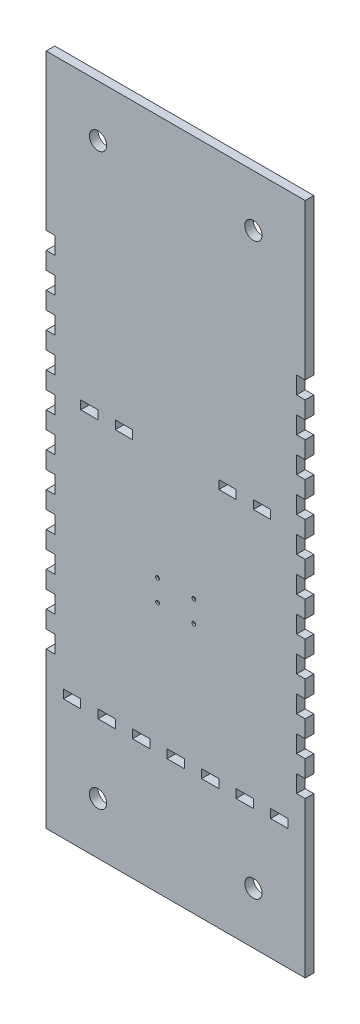
SolidWorks part; units mm, degrees
material "Balsa"
ref_plane "Alzado" through (0, 0, 0) normal (0, 0, 1) x (1, 0, 0)
ref_plane "Planta" through (0, 0, 0) normal (0, 1, 0) x (1, 0, 0)
ref_plane "Vista lateral" through (0, 0, 0) normal (1, 0, 0) x (0, 0, -1)
sketch "Croquis1" plane through (0, 0, 0) normal (0, 0, 1) x (1, 0, 0)
  line L0 (75, 0) -> (-75, 0) construction
  line L1 (75, -195) -> (-75, -195)
  line L2 (75, -195) -> (75, 195)
  line L3 (75, 195) -> (-75, 195)
  line L4 (-75, -195) -> (-75, 195)
  line L5 (75, -195) -> (-75, 195) construction
  line L6 (75, 195) -> (-75, -195) construction
  circle A0 centre (-45, 165) radius 5
  circle A1 centre (45, 165) radius 5
  circle A2 centre (-45, -165) radius 5
  circle A3 centre (45, -165) radius 5
  point P0 (0, 0)
  dimension "D3" = 10
  dimension "D8" = 10
  dimension "D1" = 150
  dimension "D2" = 390
  dimension "D4" = 30
  dimension "D5" = 30
  dimension "D6" = 30
  dimension "D7" = 30
extrude "Saliente-Extruir1" add sketch "Croquis1" along normal blind 5
sketch "Croquis3" plane through (0, 0, 0) normal (0, 0, -1) x (-1, 0, 0)
  line L0 (-75, -195) -> (-75, 195) construction
  line L1 (-75, 105) -> (-70, 105)
  line L2 (-75, 105) -> (-75, 95)
  line L3 (-75, 95) -> (-70, 95)
  line L4 (-70, 105) -> (-70, 95)
  line L5 (-75, 195) -> (75, 195) construction
  line L6 (-75, 85) -> (-75, 75)
  line L7 (-75, 85) -> (-70, 85)
  line L8 (-70, 85) -> (-70, 75)
  line L9 (-75, 75) -> (-70, 75)
  line L10 (-75, 65) -> (-75, 55)
  line L11 (-75, 65) -> (-70, 65)
  line L12 (-70, 65) -> (-70, 55)
  line L13 (-75, 55) -> (-70, 55)
  line L14 (-75, 45) -> (-75, 35)
  line L15 (-75, 45) -> (-70, 45)
  line L16 (-70, 45) -> (-70, 35)
  line L17 (-75, 35) -> (-70, 35)
  line L18 (-75, 25) -> (-75, 15)
  line L19 (-75, 25) -> (-70, 25)
  line L20 (-70, 25) -> (-70, 15)
  line L21 (-75, 15) -> (-70, 15)
  line L22 (-75, 5) -> (-75, -5)
  line L23 (-75, 5) -> (-70, 5)
  line L24 (-70, 5) -> (-70, -5)
  line L25 (-75, -5) -> (-70, -5)
  line L26 (-75, -15) -> (-75, -25)
  line L27 (-75, -15) -> (-70, -15)
  line L28 (-70, -15) -> (-70, -25)
  line L29 (-75, -25) -> (-70, -25)
  line L30 (-75, -35) -> (-75, -45)
  line L31 (-75, -35) -> (-70, -35)
  line L32 (-70, -35) -> (-70, -45)
  line L33 (-75, -45) -> (-70, -45)
  line L34 (-75, -55) -> (-75, -65)
  line L35 (-75, -55) -> (-70, -55)
  line L36 (-70, -55) -> (-70, -65)
  line L37 (-75, -65) -> (-70, -65)
  line L38 (-75, -75) -> (-75, -85)
  line L39 (-75, -75) -> (-70, -75)
  line L40 (-70, -75) -> (-70, -85)
  line L41 (-75, -85) -> (-70, -85)
  line L42 (-75, -95) -> (-75, -105)
  line L43 (-75, -95) -> (-70, -95)
  line L44 (-70, -95) -> (-70, -105)
  line L45 (-75, -105) -> (-70, -105)
  line L47 (-98.3206, -125) -> (133.2182, -125) construction
  line L48 (75, -105) -> (70, -105)
  line L49 (70, -95) -> (70, -105)
  line L50 (75, -95) -> (70, -95)
  line L51 (75, -95) -> (75, -105)
  line L52 (75, -85) -> (70, -85)
  line L53 (70, -75) -> (70, -85)
  line L54 (75, -75) -> (70, -75)
  line L55 (75, -75) -> (75, -85)
  line L56 (75, -65) -> (70, -65)
  line L57 (70, -55) -> (70, -65)
  line L58 (75, -55) -> (70, -55)
  line L59 (75, -55) -> (75, -65)
  line L60 (75, -45) -> (70, -45)
  line L61 (70, -35) -> (70, -45)
  line L62 (75, -35) -> (70, -35)
  line L63 (75, -35) -> (75, -45)
  line L64 (75, -25) -> (70, -25)
  line L65 (70, -15) -> (70, -25)
  line L66 (75, -15) -> (70, -15)
  line L67 (75, -15) -> (75, -25)
  line L68 (75, -5) -> (70, -5)
  line L69 (70, 5) -> (70, -5)
  line L70 (75, 5) -> (70, 5)
  line L71 (75, 5) -> (75, -5)
  line L72 (75, 15) -> (70, 15)
  line L73 (70, 25) -> (70, 15)
  line L74 (75, 25) -> (70, 25)
  line L75 (75, 25) -> (75, 15)
  line L76 (75, 35) -> (70, 35)
  line L77 (70, 45) -> (70, 35)
  line L78 (75, 45) -> (70, 45)
  line L79 (75, 45) -> (75, 35)
  line L80 (75, 55) -> (70, 55)
  line L81 (70, 65) -> (70, 55)
  line L82 (75, 65) -> (70, 65)
  line L83 (75, 65) -> (75, 55)
  line L84 (75, 75) -> (70, 75)
  line L85 (70, 85) -> (70, 75)
  line L86 (75, 85) -> (70, 85)
  line L87 (75, 85) -> (75, 75)
  line L88 (70, 105) -> (70, 95)
  line L89 (75, 95) -> (70, 95)
  line L90 (75, 105) -> (75, 95)
  line L91 (75, 105) -> (70, 105)
  line L92 (75, -195) -> (-75, -195) construction
  line L93 (-45, -125) -> (-45, -120)
  line L94 (-65, -125) -> (-55, -125)
  line L95 (-65, -125) -> (-65, -120)
  line L96 (-65, -120) -> (-55, -120)
  line L97 (-55, -125) -> (-55, -120)
  line L98 (-45, -125) -> (-35, -125)
  line L99 (-35, -125) -> (-35, -120)
  line L100 (-45, -120) -> (-35, -120)
  line L101 (-25, -125) -> (-25, -120)
  line L102 (-25, -125) -> (-15, -125)
  line L103 (-15, -125) -> (-15, -120)
  line L104 (-25, -120) -> (-15, -120)
  line L105 (-5, -125) -> (-5, -120)
  line L106 (-5, -125) -> (5, -125)
  line L107 (5, -125) -> (5, -120)
  line L108 (-5, -120) -> (5, -120)
  line L109 (15, -125) -> (15, -120)
  line L110 (15, -125) -> (25, -125)
  line L111 (25, -125) -> (25, -120)
  line L112 (15, -120) -> (25, -120)
  line L113 (35, -125) -> (35, -120)
  line L114 (35, -125) -> (45, -125)
  line L115 (45, -125) -> (45, -120)
  line L116 (35, -120) -> (45, -120)
  line L117 (55, -125) -> (55, -120)
  line L118 (55, -125) -> (65, -125)
  line L119 (65, -125) -> (65, -120)
  line L120 (55, -120) -> (65, -120)
  dimension "D1" = 5
  dimension "D2" = 10
  dimension "D3" = 90
  dimension "D5" = 70
  dimension "D6" = 5
  dimension "D7" = 10
  dimension "D8" = 10
  dimension "D4" = 11
  dimension "D9" = 7
extrude "Cortar-Extruir1" cut sketch "Croquis3" against normal blind 10
sketch "Croquis4" plane through (0, 0, 0) normal (0, 0, -1) x (-1, 0, 0)
  line L0 (-160.2441, 25) -> (161.5407, 25) construction
  line L1 (55, -125) -> (65, -125) construction
  line L2 (-75, 25) -> (-75, 35) construction
  line L5 (-45, 25) -> (-55, 25)
  line L6 (-45, 25) -> (-45, 30)
  line L7 (-45, 30) -> (-55, 30)
  line L8 (-55, 25) -> (-55, 30)
  line L9 (-25, 25) -> (-25, 30)
  line L10 (-25, 25) -> (-35, 25)
  line L11 (-35, 25) -> (-35, 30)
  line L12 (-25, 30) -> (-35, 30)
  line L21 (35, 25) -> (35, 30)
  line L22 (35, 25) -> (25, 25)
  line L23 (25, 25) -> (25, 30)
  line L24 (35, 30) -> (25, 30)
  line L25 (55, 25) -> (55, 30)
  line L26 (55, 25) -> (45, 25)
  line L27 (45, 25) -> (45, 30)
  line L28 (55, 30) -> (45, 30)
  line L29 (-5, 25) -> (-5, 30) [skipped]
  line L30 (-5, 30) -> (-15, 30) [skipped]
  line L31 (-15, 25) -> (-15, 30) [skipped]
  line L32 (-5, 25) -> (-15, 25) [skipped]
  line L33 (15, 25) -> (15, 30) [skipped]
  line L34 (15, 30) -> (5, 30) [skipped]
  line L35 (5, 25) -> (5, 30) [skipped]
  line L36 (15, 25) -> (5, 25) [skipped]
  dimension "D1" = 150
  dimension "D2" = 10
  dimension "D3" = 5
  dimension "D4" = 20
  dimension "D5" = 6
extrude "Cortar-Extruir2" cut sketch "Croquis4" against normal blind 10
sketch "Croquis6" plane through (0, 0, 5) normal (0, 0, 1) x (1, 0, 0)
  line L0 (0, 195) -> (0, -195) construction
  line L1 (-12.5, -35) -> (12.5, -35) construction
  line L2 (-12.5, -35) -> (-12.5, -58.862) construction
  line L3 (-12.5, -58.862) -> (12.5, -58.862) construction
  line L4 (12.5, -35) -> (12.5, -58.862) construction
  line L5 (-75, -195) -> (75, -195) construction
  line L6 (75, 195) -> (-75, 195) construction
  line L7 (25, 25) -> (35, 25) construction
  circle A0 centre (-10.5, -37) radius 1.1
  circle A1 centre (10.5, -37) radius 1.1
  circle A2 centre (10.5, -49.5) radius 1.1
  circle A3 centre (-10.5, -49.5) radius 1.1
  point P2 (0, -35)
  point P15 (0, 0)
  point P16 (0, 0)
  point P17 (0, -195)
  point P18 (-20.2763, -71.8796)
  point P19 (-16.3601, -71.8796)
  point P20 (-16.1819, -71.8796)
  point P23 (0, 195)
  dimension "D5" = 2.2
  dimension "D1" = 23.862
  dimension "D2" = 25
  dimension "D3" = 2
  dimension "D4" = 2
  dimension "D6" = 2
  dimension "D7" = 14.5
  dimension "D8" = 2
  dimension "D9" = 2
  dimension "D10" = 2
  dimension "D11" = 14.5
  dimension "D12" = 60
extrude "Cortar-Extruir7" cut sketch "Croquis6" against normal blind 1
